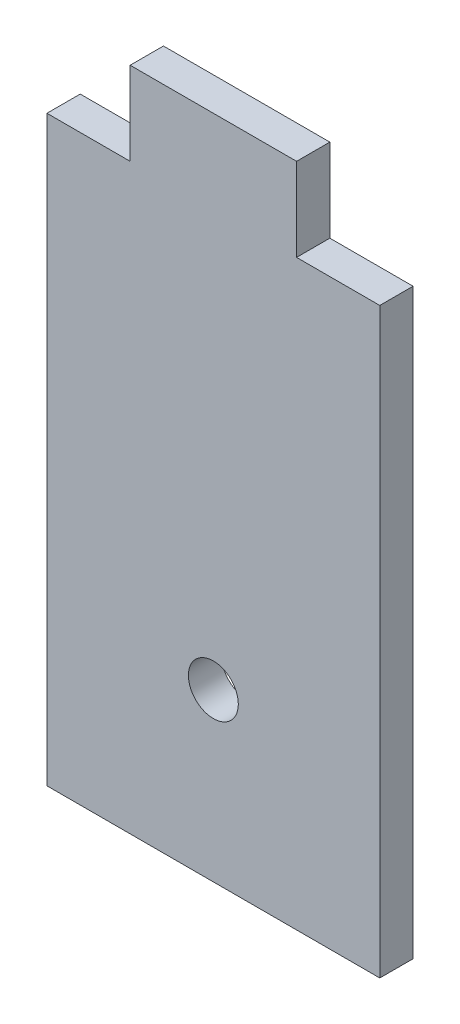
SolidWorks part; units mm, degrees
material "Acrílico (Impacto medio-alto)"
ref_plane "Alzado" through (0, 0, 0) normal (0, 0, 1) x (1, 0, 0)
ref_plane "Planta" through (0, 0, 0) normal (0, 1, 0) x (1, 0, 0)
ref_plane "Vista lateral" through (0, 0, 0) normal (1, 0, 0) x (0, 0, -1)
sketch "Croquis1" plane through (0, 0, 0) normal (0, 0, 1) x (1, 0, 0)
  line L1 (-16.9922, 17.5581) -> (-21.9922, 17.5581)
  line L2 (-21.9922, 17.5581) -> (-21.9922, -17.4419)
  line L3 (-21.9922, -17.4419) -> (-1.9922, -17.4419)
  line L4 (-1.9922, 17.5581) -> (-1.9922, -17.4419)
  line L5 (-16.9922, 22.5581) -> (-16.9922, 17.5581)
  line L6 (-6.9922, 22.5581) -> (-6.9922, 17.5581)
  line L7 (-16.9922, 22.5581) -> (-6.9922, 22.5581)
  line L8 (-6.9922, 17.5581) -> (-1.9922, 17.5581)
  circle A0 centre (-11.9922, -7.4419) radius 1.5
  dimension "D7" = 10
  dimension "D1" = 20
  dimension "D2" = 5
  dimension "D3" = 5
  dimension "D4" = 40
  dimension "D5" = 5
  dimension "D6" = 5
extrude "Saliente-Extruir1" add sketch "Croquis1" along normal blind 2
